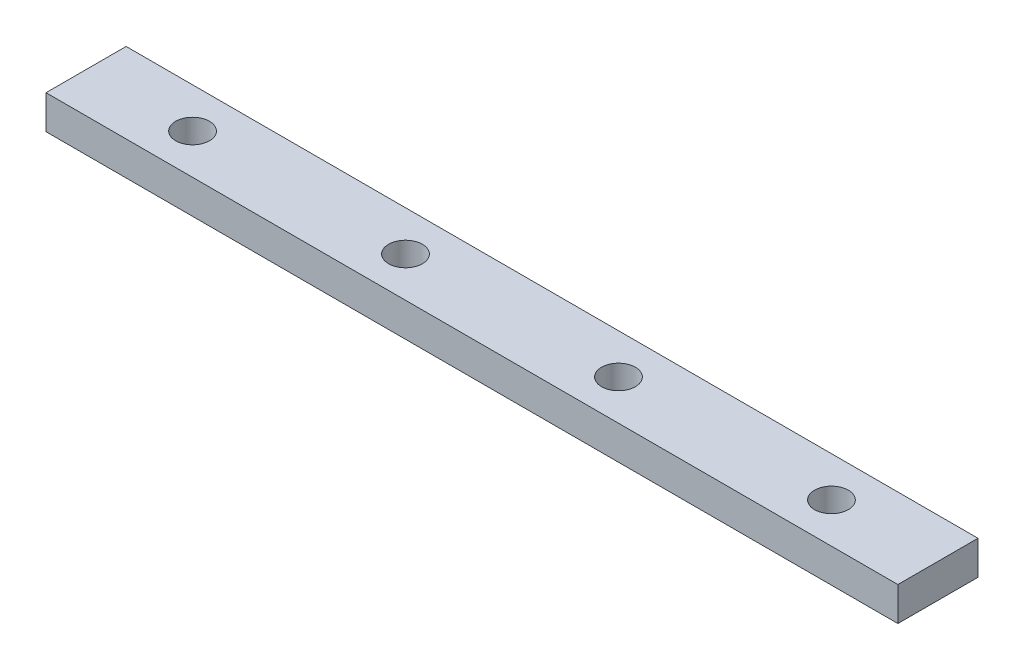
SolidWorks part; units mm, degrees
material "Plain Carbon Steel"
ref_plane "Front Plane" through (0, 0, 0) normal (0, 0, 1) x (1, 0, 0)
ref_plane "Top Plane" through (0, 0, 0) normal (0, 1, 0) x (1, 0, 0)
ref_plane "Right Plane" through (0, 0, 0) normal (1, 0, 0) x (0, 0, -1)
sketch "Sketch1" plane through (0, 0, 0) normal (1, 0, 0) x (0, 0, -1)
  line L1 (0, 0) -> (30.1, 0)
  line L2 (0, 0) -> (0, 12.7)
  line L3 (0, 12.7) -> (30.1, 12.7)
  line L4 (30.1, 0) -> (30.1, 12.7)
  dimension "D1" = 30.1
  dimension "D2" = 12.7
extrude "Boss-Extrude1" add sketch "Sketch1" along normal blind 320
sketch "Sketch2" plane through (0, 0, 0) normal (0, 0, 1) x (1, 0, 0)
  line L0 (0, 0) -> (320, 0) construction
  point P4 (160, 0)
sketch "Sketch3" plane through (0, 12.7, 0) normal (0, 1, 0) x (1, 0, 0)
  line L0 (120, 15.05) -> (40, 15.05) construction
  line L2 (120, 15.05) -> (200, 15.05) construction
  line L3 (200, 15.05) -> (280, 15.05) construction
  line L4 (280, 15.05) -> (320, 15.05) construction
  line L5 (320, 30.1) -> (320, 0) construction
  line L6 (40, 15.05) -> (0, 15.05) construction
  line L7 (0, 30.1) -> (0, 0) construction
  circle A0 centre (120, 15.05) radius 6.35
  circle A1 centre (200, 15.05) radius 6.35
  circle A2 centre (280, 15.05) radius 6.35
  circle A3 centre (40, 15.05) radius 6.35
  dimension "D1" = 12.7
  dimension "D2" = 12.7
  dimension "D3" = 12.7
  dimension "D4" = 12.7
  dimension "D5" = 40
extrude "Cut-Extrude1" cut sketch "Sketch3" against normal through all
